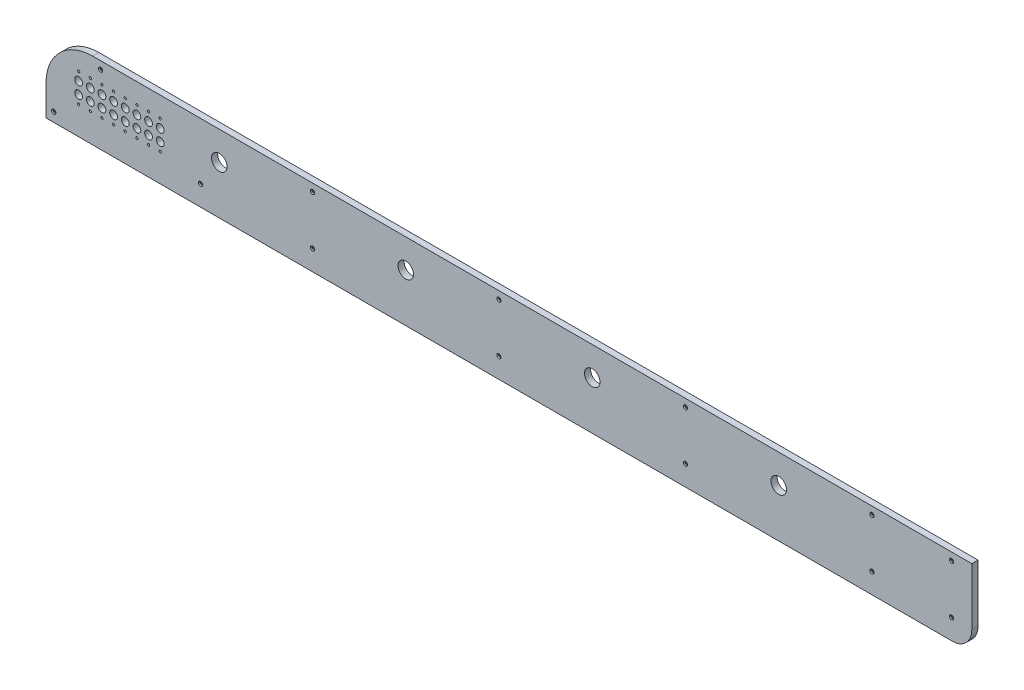
SolidWorks part; units mm, degrees
ref_plane "Plan de face" through (0, 0, 0) normal (0, 0, 1) x (1, 0, 0)
ref_plane "Plan de dessus" through (0, 0, 0) normal (0, 1, 0) x (1, 0, 0)
ref_plane "Plan de droite" through (0, 0, 0) normal (1, 0, 0) x (0, 0, -1)
sketch "Esquisse1" plane through (0, 0, 0) normal (0, 0, 1) x (1, 0, 0)
  line L1 (938.5, 261) -> (-193, 261)
  line L2 (938.5, 261) -> (938.5, 187)
  line L3 (913.5, 162) -> (-253, 162)
  line L4 (-253, 201) -> (-253, 162)
  line L5 (-253, 201) -> (-253, -141) construction
  line L6 (900, 182) -> (-60, 182) construction
  line L7 (943.5, -201) -> (943.5, 261) construction
  line L8 (190, 261) -> (420, 261) construction
  arc A0 (938.5, 187) -> (913.5, 162) centre (913.5, 187) cw
  arc A1 (-193, 261) -> (-253, 201) centre (-193, 201) ccw
  dimension "D2" = 25
  dimension "D4" = 60
  dimension "D1" = 20
  dimension "D3" = 5
extrude "Boss.-Extru.1" add sketch "Esquisse1" along normal blind 8 contours L3 L4 A1 L1 L2 A0
sketch "Esquisse3" plane through (0, 0, 8) normal (0, 0, 1) x (1, 0, 0)
  circle A0 centre (-211, 198) radius 1.5 construction
  circle A1 centre (-211, 209) radius 5 construction
  circle A2 centre (-211, 224) radius 5 construction
  circle A3 centre (-211, 235) radius 1.5 construction
  circle A4 centre (-211, 198) radius 1.5
  circle A5 centre (-211, 209) radius 5
  circle A6 centre (-211, 224) radius 5
  circle A7 centre (-211, 235) radius 1.5
  circle A8 centre (-196, 209) radius 5
  circle A9 centre (-196, 198) radius 1.5
  circle A10 centre (-196, 224) radius 5
  circle A11 centre (-196, 235) radius 1.5
  circle A12 centre (-181, 209) radius 5
  circle A13 centre (-181, 198) radius 1.5
  circle A14 centre (-181, 224) radius 5
  circle A15 centre (-181, 235) radius 1.5
  circle A16 centre (-166, 209) radius 5
  circle A17 centre (-166, 198) radius 1.5
  circle A18 centre (-166, 224) radius 5
  circle A19 centre (-166, 235) radius 1.5
  circle A20 centre (-151, 209) radius 5
  circle A21 centre (-151, 198) radius 1.5
  circle A22 centre (-151, 224) radius 5
  circle A23 centre (-151, 235) radius 1.5
  circle A24 centre (-136, 209) radius 5
  circle A25 centre (-136, 198) radius 1.5
  circle A26 centre (-136, 224) radius 5
  circle A27 centre (-136, 235) radius 1.5
  circle A28 centre (-121, 209) radius 5
  circle A29 centre (-121, 198) radius 1.5
  circle A30 centre (-121, 224) radius 5
  circle A31 centre (-121, 235) radius 1.5
  circle A32 centre (-106, 209) radius 5
  circle A33 centre (-106, 198) radius 1.5
  circle A34 centre (-106, 224) radius 5
  circle A35 centre (-106, 235) radius 1.5
  dimension "D1" = 8
extrude "Enlèv. mat.-Extru.1" cut sketch "Esquisse3" against normal through all
sketch "Esquisse4" plane through (0, 0, 8) normal (0, 0, 1) x (1, 0, 0)
  line L0 (-60, 181) -> (-60, -181) construction
  line L1 (938.5, 261) -> (-193, 261) construction
  circle A0 centre (-30, 224) radius 10
  circle A1 centre (210, 224) radius 10
  circle A2 centre (450, 224) radius 10
  circle A3 centre (690, 224) radius 10
  dimension "D1" = 20
  dimension "D2" = 30
  dimension "D3" = 37
  dimension "D5" = 240
  dimension "D4" = 4
extrude "Enlèv. mat.-Extru.2" cut sketch "Esquisse4" against normal through all
hole_wizard "Chambrage pour vis à tête cylindrique courte six pans creux M31" positions "Esquisse5" profile "Esquisse6" counterbore size "M3" standard "DIN" end condition through all
sketch "Esquisse5" plane through (0, 0, 8) normal (0, 0, 1) x (1, 0, 0)
  line L0 (900, 182) -> (-60, 182) construction
  line L1 (-60, 182) -> (-60, 195) construction
  line L2 (-253, 201) -> (-253, 162) construction
  line L3 (913.5, 162) -> (-253, 162) construction
  line L4 (-30, 224) -> (210, 224) construction
  line L6 (210, 224) -> (450, 224) construction
  line L7 (450, 224) -> (690, 224) construction
  line L11 (330, 188) -> (570, 188) construction
  line L12 (570, 188) -> (810, 188) construction
  line L14 (938.5, 261) -> (938.5, 187) construction
  line L15 (938.5, 261) -> (-193, 261) construction
  point P0 (-54, 188)
  point P2 (90, 188)
  point P4 (330, 188)
  point P6 (570, 188)
  point P8 (810, 188)
  point P10 (912.5, 188)
  point P12 (912.5, 251)
  point P14 (810, 251)
  point P16 (570, 251)
  point P18 (330, 251)
  point P20 (90, 251)
  point P22 (-243, 174)
  point P24 (-182.7687, 251)
  point P65 (90, 224)
  point P67 (330, 224)
  point P69 (570, 224)
  dimension "D1" = 6
  dimension "D2" = 6
  dimension "D3" = 10
  dimension "D4" = 12
  dimension "D5" = 26
  dimension "D6" = 10
sketch "Esquisse6" plane through (-54, 188, 8) normal (1, 0, 0) x (0, -1, 0)
  line L0 (0, 0) -> (0, 8)
  line L1 (0, 8) -> (1.5, 8)
  line L3 (1.5, 8) -> (1.5, 2)
  line L4 (1.5, 2) -> (2.75, 2)
  line L5 (2.75, 2) -> (2.75, 0)
  line L7 (2.75, 0) -> (0, 0)
  line L11 (0, -6.35) -> (0, 107.95) construction
  dimension "Diamètre du perçage jusqu'au prochain" = 3
  dimension "Profondeur du perçage jusqu'au prochain" = 8
  dimension "Diamètre du chambrage" = 5.5
  dimension "Profondeur du chambrage" = 2
